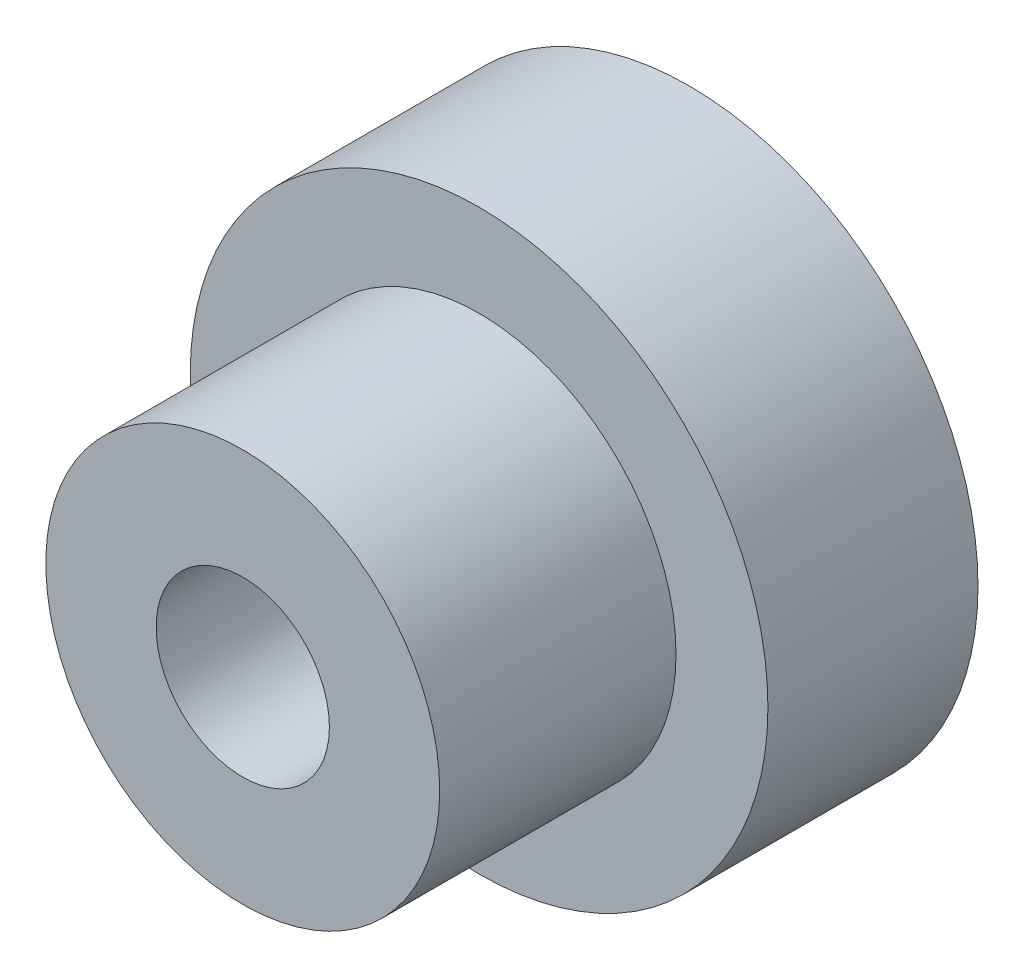
SolidWorks part; units mm, degrees
ref_plane "Front Plane" through (0, 0, 0) normal (0, 0, 1) x (1, 0, 0)
ref_plane "Top Plane" through (0, 0, 0) normal (0, 1, 0) x (1, 0, 0)
ref_plane "Right Plane" through (0, 0, 0) normal (1, 0, 0) x (0, 0, -1)
sketch "Sketch1" plane through (0, 0, 0) normal (0, 0, 1) x (1, 0, 0)
  circle A0 centre (0, 0) radius 11
  dimension "D1" = 22
extrude "Boss-Extrude1" add sketch "Sketch1" along normal blind 8
sketch "Sketch2" plane through (0, 0, 8) normal (0, 0, 1) x (1, 0, 0)
  circle A0 centre (0, 0) radius 7.5
  dimension "D1" = 15
extrude "Boss-Extrude2" add sketch "Sketch2" along normal blind 9
sketch "Sketch3" plane through (0, 0, 17) normal (0, 0, 1) x (1, 0, 0)
  circle A0 centre (0, 0) radius 3.3
  dimension "D1" = 6.6
extrude "Cut-Extrude1" cut sketch "Sketch3" against normal through all
